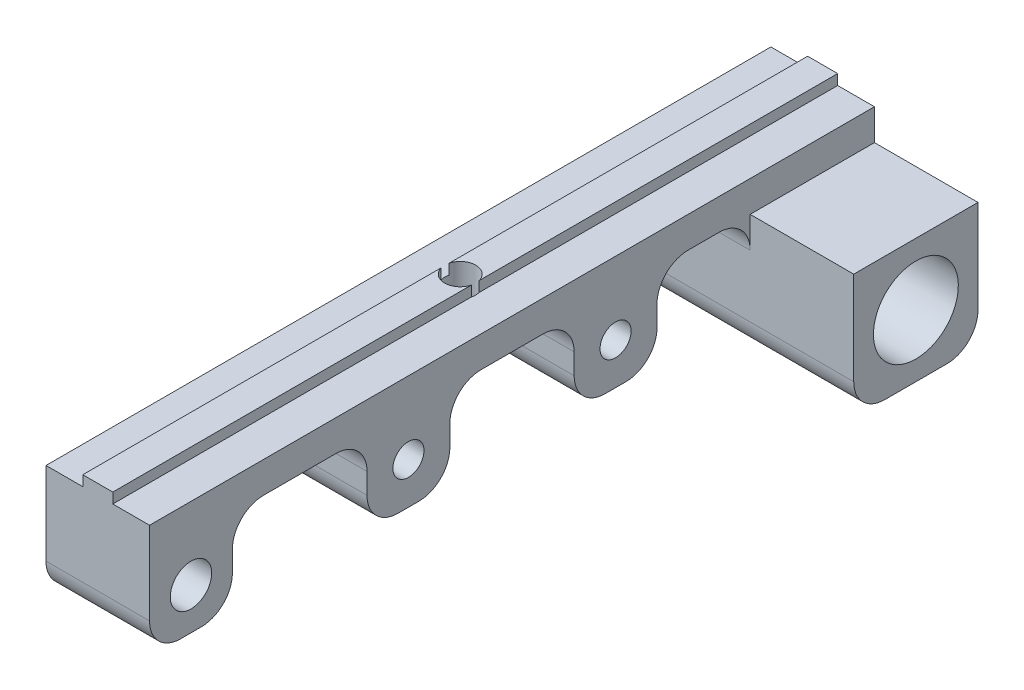
SolidWorks part; units mm, degrees
ref_plane "Front Plane" through (0, 0, 0) normal (0, 0, 1) x (1, 0, 0)
ref_plane "Top Plane" through (0, 0, 0) normal (0, 1, 0) x (1, 0, 0)
ref_plane "Right Plane" through (0, 0, 0) normal (1, 0, 0) x (0, 0, -1)
sketch "Sketch1" plane through (0, 0, 0) normal (0, 0, 1) x (1, 0, 0)
  line L0 (-5, 0) -> (5, 0)
  line L1 (5, 0) -> (5, 3)
  line L2 (5, 3) -> (1.45, 3)
  line L3 (1.45, 3) -> (1.45, 4)
  line L4 (1.45, 4) -> (-1.45, 4)
  line L5 (-1.45, 4) -> (-1.45, 3)
  line L6 (-1.45, 3) -> (-5, 3)
  line L7 (-5, 3) -> (-5, 0)
  point P9 (0, 0)
  point P10 (0, 0)
  dimension "D1" = 10
  dimension "D2" = 2.9
  dimension "D3" = 3
  dimension "D4" = 1
extrude "MakerBeamFix" add sketch "Sketch1" along normal mid plane 70
sketch "Sketch2" plane through (0, 0, 0) normal (0, -1, 0) x (-1, 0, 0)
  circle A0 centre (0, 0) radius 1.5
  point P2 (0, 0)
  dimension "D1" = 3
extrude "MakerBeamFixHole" cut sketch "Sketch2" against normal through all
sketch "Sketch3" plane through (-5, 0, 0) normal (-1, 0, 0) x (0, 0, 1)
  line L1 (-23, -12) -> (-35, -12)
  line L2 (-23, -12) -> (-23, 0)
  line L3 (-23, 0) -> (-35, 0)
  line L4 (-35, -12) -> (-35, 0)
  line L5 (-23, -12) -> (-35, 0) construction
  line L6 (-23, 0) -> (-35, -12) construction
  circle A0 centre (-29, -6) radius 4.1
  point P0 (-29, -6)
  dimension "D1" = 8.2
  dimension "D2" = 12
  dimension "D3" = 12
extrude "MakerBeamToolBigHexaScrewDriver" add sketch "Sketch3" against normal blind 20
sketch "Sketch4" plane through (-5, 0, 0) normal (-1, 0, 0) x (0, 0, 1)
  line L0 (35, 0) -> (-23, 0) construction
  line L1 (-14, 0) -> (-6, 0)
  line L2 (-14, 0) -> (-14, -8)
  line L3 (-14, -8) -> (-6, -8)
  line L4 (-6, 0) -> (-6, -8)
  line L5 (-14, 0) -> (-6, -8) construction
  line L6 (-14, -8) -> (-6, 0) construction
  line L7 (-35, 3) -> (-35, -12) construction
  circle A0 centre (-10, -4) radius 1.5
  point P0 (-10, -4)
  point P5 (-17.0865, -3.7732)
  dimension "D1" = 3
  dimension "D2" = 8
  dimension "D3" = 25
extrude "MakerBeamToolSmallHexaScrewDriver" add sketch "Sketch4" against normal blind 10
pattern_linear "SimpleScrewDriver3mm" count 2 spacing 20 along (0, 0, 1) of "MakerBeamToolSmallHexaScrewDriver"
sketch "Sketch5" plane through (-5, 0, 0) normal (-1, 0, 0) x (0, 0, 1)
  line L0 (35, 0) -> (14, 0) construction
  line L1 (27, 0) -> (35, 0)
  line L2 (27, 0) -> (27, -8)
  line L3 (27, -8) -> (35, -8)
  line L4 (35, 0) -> (35, -8)
  line L5 (27, 0) -> (35, -8) construction
  line L6 (27, -8) -> (35, 0) construction
  line L7 (35, 3) -> (35, 0) construction
  circle A0 centre (31, -4) radius 2
  point P0 (31, -4)
  dimension "D2" = 4
  dimension "D1" = 8
extrude "Boss-Extrude4" add sketch "Sketch5" against normal blind 10
fillet "Fillet1" radius 3 14 edges at (5, -12, -35) (0, 0, -14) (0, 0, 6) (0, 0, 27) (0, -8, 35) (0, -8, 27) (0, 0, 14) (0, -8, 14) (0, -8, 6) (0, 0, -6) (0, -8, -6) (0, -8, -14) (0, 0, -23) (5, -12, -23)
